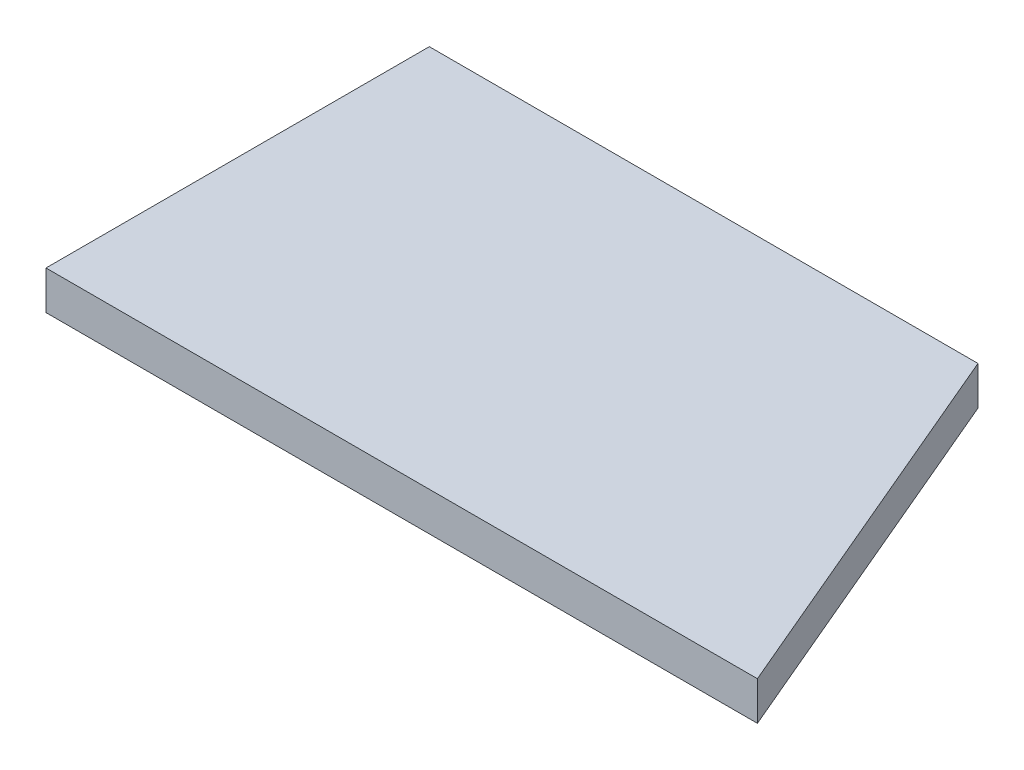
SolidWorks part; units mm, degrees
ref_plane "Спереди" through (0, 0, 0) normal (0, 0, 1) x (1, 0, 0)
ref_plane "Сверху" through (0, 0, 0) normal (0, 1, 0) x (1, 0, 0)
ref_plane "Справа" through (0, 0, 0) normal (1, 0, 0) x (0, 0, -1)
sketch "Эскиз1" plane through (0, 0, 0) normal (0, 1, 0) x (1, 0, 0)
  line L0 (0, 0) -> (92, 0)
  line L1 (92, 0) -> (70.9585, 49.5707)
  line L2 (70.9585, 49.5707) -> (0, 49.5707)
  line L3 (0, 49.5707) -> (0, 0)
extrude "Бобышка-Вытянуть1" add sketch "Эскиз1" along normal blind 5
